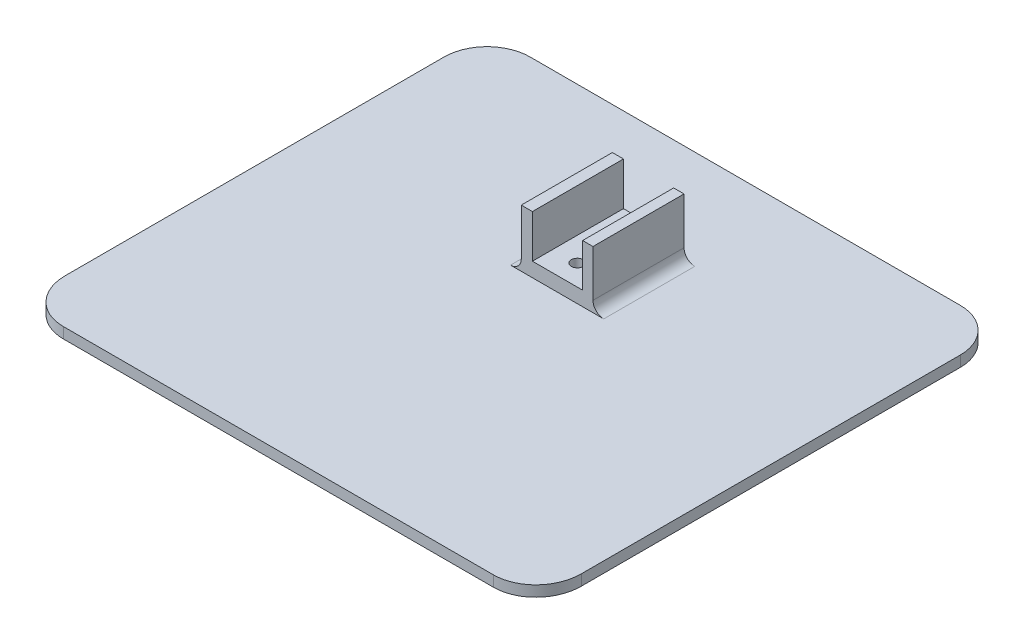
SolidWorks part; units mm, degrees
ref_plane "Front Plane" through (0, 0, 0) normal (0, 0, 1) x (1, 0, 0)
ref_plane "Top Plane" through (0, 0, 0) normal (0, 1, 0) x (1, 0, 0)
ref_plane "Right Plane" through (0, 0, 0) normal (1, 0, 0) x (0, 0, -1)
sketch "Sketch1" plane through (0, 0, 0) normal (0, 1, 0) x (1, 0, 0)
  line L5 (-4.9801, 26.114) -> (5.0718, 26.114) construction
  line L6 (-4.9801, 26.114) -> (-4.9801, 8.114) construction
  line L7 (-4.9801, 8.114) -> (5.0718, 8.114) construction
  line L8 (5.0718, 26.114) -> (5.0718, 8.114) construction
  line L17 (-68.2852, 55.1401) -> (68.98, -60.6983) construction
  line L18 (-68.2852, -60.6983) -> (68.98, 55.1401) construction
  line L22 (-72.3912, 44.9655) -> (-72.3912, -60.7356)
  line L23 (-60.3912, -73.259) -> (59.6088, -73.259)
  line L24 (71.6088, -60.7356) -> (71.6088, 44.9655)
  line L25 (59.6088, 56.9655) -> (-60.3912, 56.9655)
  circle A0 centre (0.2087, 24.378) radius 1.6559
  circle A1 centre (-0.0197, 9.7626) radius 1.6559
  arc A8 (71.6088, 44.9655) -> (59.6088, 56.9655) centre (59.6088, 44.9655) ccw
  arc A9 (-60.3912, 56.9655) -> (-72.3912, 44.9655) centre (-60.3912, 44.9655) ccw
  spline S2 degree 3 poles (-72.3912, -60.7356) (-72.3912, -61.9921) (-72.1318, -63.8413) (-71.1931, -66.3312) (-70.1158, -68.1935) (-68.6029, -69.9902) (-66.871, -71.3562) (-65.1678, -72.2641) (-63.672, -72.8225) (-62.0831, -73.171) (-60.9506, -73.259) (-60.3912, -73.259) knots 0 0 0 0 0.25 0.375 0.5 0.625 0.75 0.8125 0.875 0.9375 1 1 1 1
  spline S3 degree 3 poles (59.6088, -73.259) (60.1618, -73.259) (61.2792, -73.174) (62.8603, -72.8307) (64.3487, -72.28) (66.0618, -71.3753) (67.8044, -70.0062) (69.8226, -67.6167) (71.259, -64.4791) (71.6088, -61.9993) (71.6088, -60.7356) knots 0 0 0 0 0.0625 0.125 0.1875 0.25 0.375 0.5 0.75 1 1 1 1
  point P4 (0.3474, -2.7791)
  dimension "D1" = 18
extrude "Boss-Extrude1" add sketch "Sketch1" along normal blind 3
sketch "Sketch2" plane through (0, 3, 0) normal (0, 1, 0) x (1, 0, 0)
  line L1 (-9.8384, 29.3484) -> (10.1616, 29.3484)
  line L2 (-9.8384, 29.3484) -> (-9.8384, 3.9488)
  line L3 (-9.8384, 3.9488) -> (10.1616, 3.9488)
  line L4 (10.1616, 29.3484) -> (10.1616, 3.9488)
  circle A0 centre (0.2087, 24.378) radius 1.6559 construction
  circle A1 centre (-0.0197, 9.7626) radius 1.6559 construction
  circle A2 centre (-0.0197, 9.7626) radius 1.6559
  circle A3 centre (0.2087, 24.378) radius 1.6559
  dimension "D1" = 20
extrude "Boss-Extrude2" add sketch "Sketch2" along normal blind 16
sketch "Sketch3" plane through (0, 19, 0) normal (0, 1, 0) x (1, 0, 0)
  line L1 (-6.731, 31.8785) -> (7.269, 31.8785)
  line L2 (-6.731, 31.8785) -> (-6.731, 1.4449)
  line L3 (-6.731, 1.4449) -> (7.269, 1.4449)
  line L4 (7.269, 31.8785) -> (7.269, 1.4449)
  dimension "D1" = 14
extrude "Cut-Extrude1" cut sketch "Sketch3" against normal blind 12 contours L2 L1 L4 L3
fillet "Fillet1" radius 3 2 edges at (10.1616, 3, -16.6486) (-9.8384, 3, -16.6486)
sketch "Sketch4" plane through (0, 0, 0) normal (0, -1, 0) x (1, 0, 0)
  circle A11 centre (-0.0197, -9.7626) radius 3.6559
  circle A12 centre (-0.0197, -9.7626) radius 3.6559
  circle A14 centre (0.2087, -24.378) radius 3.6559
  circle A15 centre (0.2087, -24.378) radius 3.6559
  dimension "D1" = 2
  dimension "D2" = 2
extrude "Cut-Extrude2" cut sketch "Sketch4" against normal blind 3
